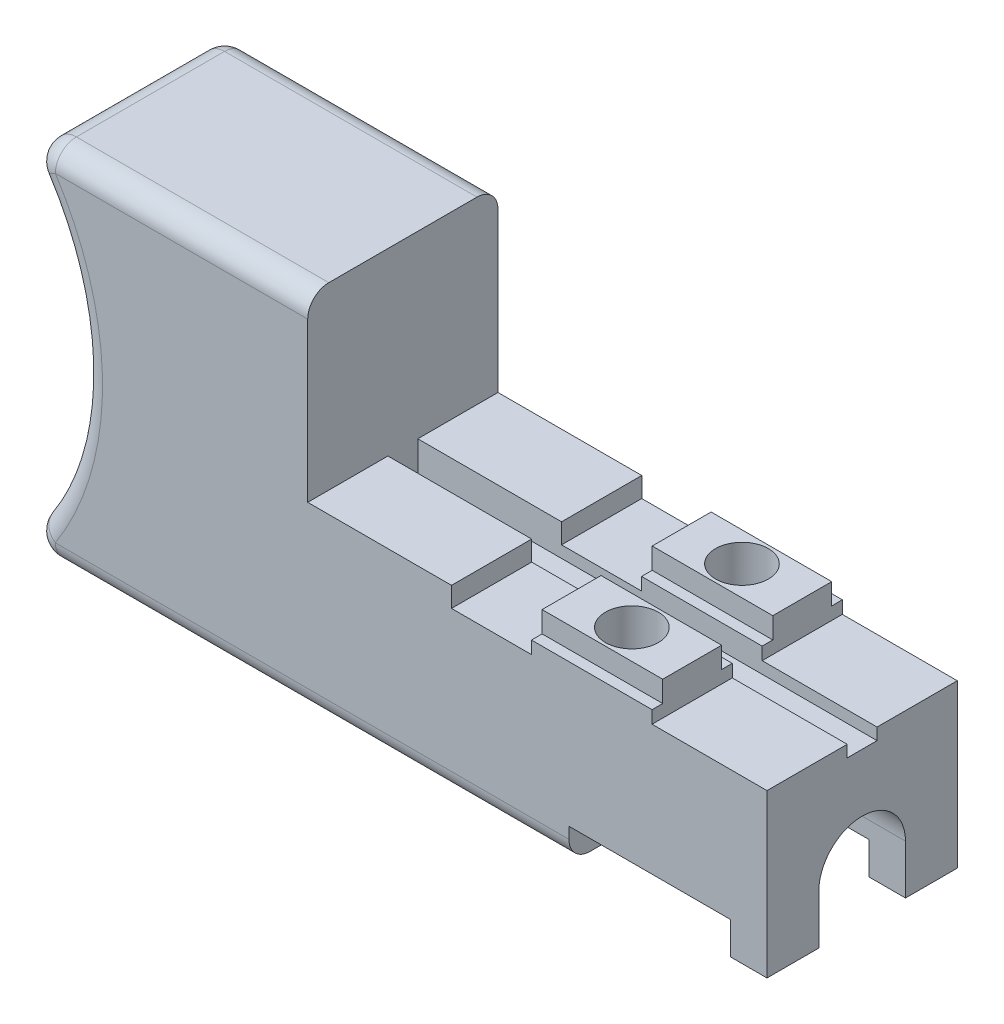
SolidWorks part; units mm, degrees
ref_plane "Front Plane" through (0, 0, 0) normal (0, 0, 1) x (1, 0, 0)
ref_plane "Top Plane" through (0, 0, 0) normal (0, 1, 0) x (1, 0, 0)
ref_plane "Right Plane" through (0, 0, 0) normal (1, 0, 0) x (0, 0, -1)
sketch "Sketch1" plane through (0, 0, 0) normal (0, 0, 1) x (1, 0, 0)
  line L0 (0, 0) -> (8.6741, 0)
  line L1 (8.6741, 0) -> (8.6741, -1.2065)
  line L2 (8.6741, -1.2065) -> (13.5001, -1.2065)
  line L3 (13.5001, -1.2065) -> (13.5001, 0.8255)
  line L4 (13.5001, 0.8255) -> (20.7772, 0.8255)
  line L5 (20.7772, 0.8255) -> (20.7772, -1.2065)
  line L6 (20.7772, -1.2065) -> (27.7114, -1.2065)
  line L7 (27.7114, -1.2065) -> (27.7114, -11)
  line L8 (27.7114, -11) -> (25.5016, -11)
  line L9 (25.5016, -11) -> (25.5016, -9.0442)
  line L10 (25.5016, -9.0442) -> (15.7607, -9.0442)
  line L11 (15.7607, -9.0442) -> (15.7607, -11)
  line L12 (15.7607, -11) -> (0, -11)
  line L13 (0, -11) -> (0, 0)
  dimension "D1" = 11
  dimension "D2" = 27.7114
  dimension "D3" = 2.2098
  dimension "D4" = 9.7409
  dimension "D5" = 1.9558
  dimension "D6" = 6.9342
  dimension "D7" = 7.2771
  dimension "D8" = 2.032
  dimension "D9" = 1.2065
  dimension "D10" = 4.826
extrude "Boss-Extrude1" add sketch "Sketch1" against normal blind 11.4808
sketch "Sketch2" plane through (0, 0.8255, 0) normal (0, 1, 0) x (1, 0, 0)
  line L0 (0, 11.4808) -> (0, 0) construction
  line L1 (0, 4.8387) -> (27.7114, 4.8387)
  line L2 (0, 4.8387) -> (0, 6.6421)
  line L3 (0, 6.6421) -> (27.7114, 6.6421)
  line L4 (27.7114, 4.8387) -> (27.7114, 6.6421)
  line L5 (27.7114, 11.4808) -> (27.7114, 0) construction
  point P9 (0, 5.7404)
  point P10 (0, 5.7404)
  dimension "D1" = 1.8034
extrude "Cut-Extrude1" cut sketch "Sketch2" against normal blind 2.7432
sketch "Sketch3" plane through (0, 0.8255, 0) normal (0, 1, 0) x (1, 0, 0)
  line L0 (13.5001, 11.4808) -> (13.5001, 6.6421) construction
  line L1 (13.5001, 4.8387) -> (13.5001, 0) construction
  line L2 (20.7772, 11.4808) -> (13.5001, 11.4808) construction
  circle A0 centre (17.1386, 9.0615) radius 1.5938
  circle A1 centre (17.1386, 2.4193) radius 1.5938
  point P7 (13.5001, 9.0615)
  point P10 (13.5001, 2.4193)
  point P13 (17.1386, 11.4808)
  dimension "D1" = 3.1877
extrude "Cut-Extrude2" cut sketch "Sketch3" against normal blind 7.112
sketch "Sketch4" plane through (0, 0, 0) normal (0, 0, 1) x (1, 0, 0)
  line L0 (0, 10.844) -> (0, -11)
  line L1 (0, -11) -> (-17.78, -11)
  line L2 (0, 10.844) -> (-17.78, 10.844)
  line L4 (0, -11) -> (15.7607, -11) construction
  arc A0 (-17.78, -11) -> (-17.78, 10.844) centre (-30.161, -0.078) ccw
  dimension "D2" = 16.51
  dimension "D1" = 21.844
  dimension "D4" = 17.78
extrude "Boss-Extrude2" add sketch "Sketch4" against normal up to surface (11.4808 mm away) up to face at (15.9893, -4.6617, -11.4808)
fillet "Fillet1" radius 1.27 8 edges at (-13.651, -0.078, 0) (-13.651, -0.078, -11.4808) (-1.0096, -11, -11.4808) (-8.89, 10.844, -11.4808) (-8.89, 10.844, 0) (-1.0096, -11, 0) (-17.78, -11, -5.7404) (-17.78, 10.844, -5.7404)
sketch "Sketch5" plane through (0, 0.8255, 0) normal (0, 1, 0) x (1, 0, 0)
  line L0 (27.7114, 5.7404) -> (0, 5.7404) construction
  line L1 (13.5001, 6.6421) -> (20.7772, 6.6421)
  line L2 (13.5001, 6.6421) -> (13.5001, 7.2835)
  line L3 (13.5001, 11.4808) -> (20.7772, 11.4808)
  line L4 (20.7772, 6.6421) -> (20.7772, 7.2835)
  line L5 (13.5001, 7.2835) -> (20.7772, 7.2835)
  line L7 (13.5001, 10.8395) -> (20.7772, 10.8395)
  line L9 (27.7114, 4.8387) -> (27.7114, 6.6421) construction
  line L10 (0, 10.2108) -> (0, 1.27) construction
  line L11 (13.5001, 0) -> (20.7772, 0)
  line L12 (20.7772, 4.8387) -> (20.7772, 4.1974)
  line L13 (13.5001, 4.8387) -> (20.7772, 4.8387)
  line L14 (13.5001, 4.8387) -> (13.5001, 4.1973)
  line L15 (13.5001, 0.6413) -> (20.7772, 0.6414)
  line L17 (13.5001, 4.1973) -> (20.7772, 4.1974)
  line L19 (13.5001, 10.8395) -> (13.5001, 11.4808)
  line L20 (20.7772, 10.8395) -> (20.7772, 11.4808)
  line L21 (13.5001, 0.6413) -> (13.5001, 0)
  line L22 (20.7772, 0.6414) -> (20.7772, 0)
  dimension "D1" = 3.556
extrude "Cut-Extrude3" cut sketch "Sketch5" against normal blind 1.27
sketch "Sketch6" plane through (27.7114, 0, 0) normal (1, 0, 0) x (0, 0, -1)
  line L0 (3.1242, -11) -> (3.1242, -8.0282)
  line L1 (11.4808, -11) -> (0, -11) construction
  line L2 (8.3566, -8.0282) -> (8.3566, -11)
  line L3 (8.3566, -11) -> (3.1242, -11)
  arc A0 (3.1242, -8.0282) -> (8.3566, -8.0282) centre (5.7404, -8.0282) cw
  point P7 (5.7404, -11)
  point P9 (5.7404, -11)
  dimension "D2" = 5.588
  dimension "D1" = 5.2324
extrude "Cut-Extrude4" cut sketch "Sketch6" against normal blind 13.589
